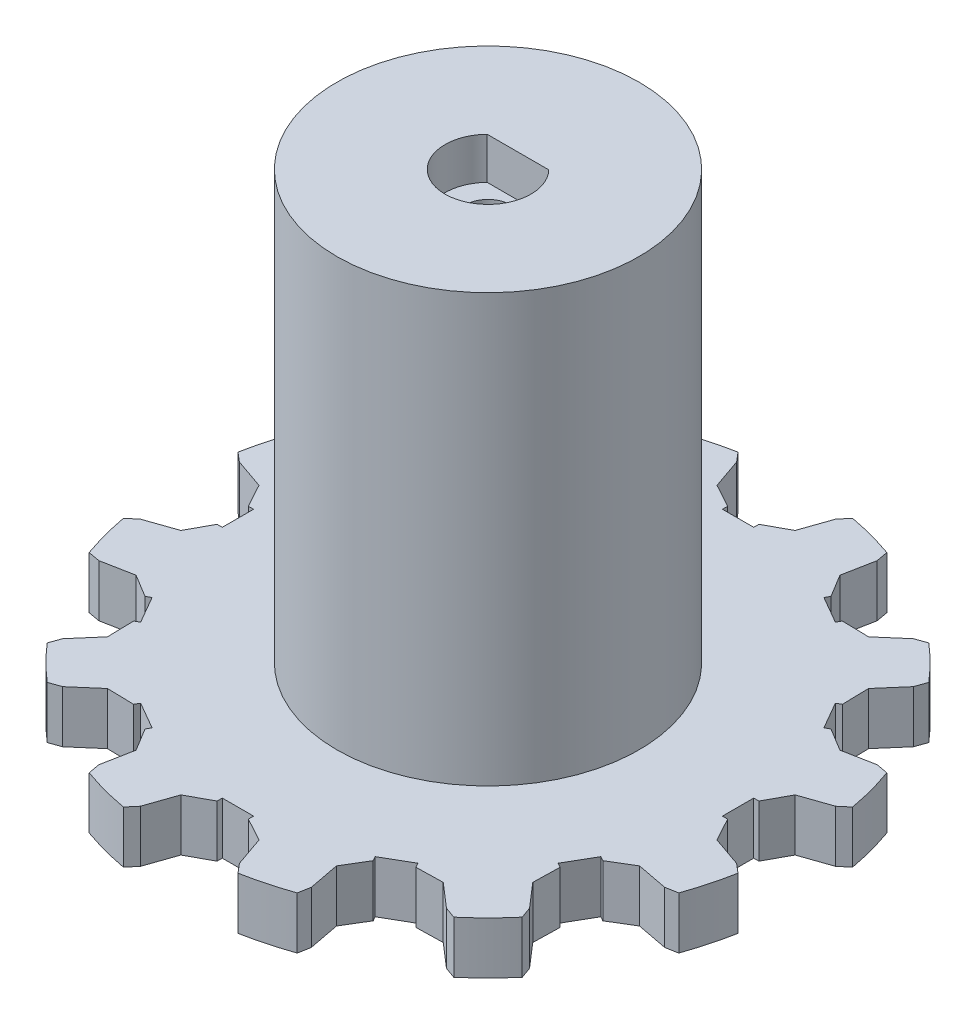
SolidWorks part; units mm, degrees
ref_plane "Front Plane" through (0, 0, 0) normal (0, 0, 1) x (1, 0, 0)
ref_plane "Top Plane" through (0, 0, 0) normal (0, 1, 0) x (1, 0, 0)
ref_plane "Right Plane" through (0, 0, 0) normal (1, 0, 0) x (0, 0, -1)
sketch "Sketch1" plane through (0, 0, 0) normal (0, 1, 0) x (1, 0, 0)
  line L0 (0, -1000) -> (0, 49000) construction
  line L1 (-3.75, 25.7281) -> (-4.75, 28.6083)
  line L2 (3.75, 25.7281) -> (4.75, 28.6083)
  line L3 (-3.75, 25.7281) -> (-1.5, 24.4948)
  line L4 (1.5, 24) -> (-1.5, 24)
  line L8 (-1.5, 24) -> (-1.5, 24.4948)
  line L9 (1.5, 24) -> (1.5, 24.4948)
  line L10 (3.75, 25.7281) -> (1.5, 24.4948)
  line L11 (4.75, 28.6083) -> (5.5, 29.4915)
  line L12 (-4.75, 28.6083) -> (-5.5, 29.4915)
  line L13 (18.4178, 22.4006) -> (19.5089, 22.7904)
  line L14 (16.1117, 20.4062) -> (18.4178, 22.4006)
  line L15 (16.1117, 20.4062) -> (13.5464, 20.4631)
  line L16 (13.299, 20.0346) -> (13.5464, 20.4631)
  line L17 (13.299, 20.0346) -> (10.701, 21.5346)
  line L18 (10.701, 21.5346) -> (10.9484, 21.9631)
  line L19 (9.6165, 24.1562) -> (10.9484, 21.9631)
  line L20 (9.6165, 24.1562) -> (10.1906, 27.1506)
  line L21 (10.1906, 27.1506) -> (9.9826, 28.2904)
  line L22 (27.1506, 10.1906) -> (28.2904, 9.9826)
  line L23 (24.1562, 9.6165) -> (27.1506, 10.1906)
  line L24 (24.1562, 9.6165) -> (21.9631, 10.9484)
  line L25 (21.5346, 10.701) -> (21.9631, 10.9484)
  line L26 (21.5346, 10.701) -> (20.0346, 13.299)
  line L27 (20.0346, 13.299) -> (20.4631, 13.5464)
  line L28 (20.4062, 16.1117) -> (20.4631, 13.5464)
  line L29 (20.4062, 16.1117) -> (22.4006, 18.4178)
  line L30 (22.4006, 18.4178) -> (22.7904, 19.5089)
  line L31 (28.6083, -4.75) -> (29.4915, -5.5)
  line L32 (25.7281, -3.75) -> (28.6083, -4.75)
  line L33 (25.7281, -3.75) -> (24.4948, -1.5)
  line L34 (24, -1.5) -> (24.4948, -1.5)
  line L35 (24, -1.5) -> (24, 1.5)
  line L36 (24, 1.5) -> (24.4948, 1.5)
  line L37 (25.7281, 3.75) -> (24.4948, 1.5)
  line L38 (25.7281, 3.75) -> (28.6083, 4.75)
  line L39 (28.6083, 4.75) -> (29.4915, 5.5)
  line L40 (22.4006, -18.4178) -> (22.7904, -19.5089)
  line L41 (20.4062, -16.1117) -> (22.4006, -18.4178)
  line L42 (20.4062, -16.1117) -> (20.4631, -13.5464)
  line L43 (20.0346, -13.299) -> (20.4631, -13.5464)
  line L44 (20.0346, -13.299) -> (21.5346, -10.701)
  line L45 (21.5346, -10.701) -> (21.9631, -10.9484)
  line L46 (24.1562, -9.6165) -> (21.9631, -10.9484)
  line L47 (24.1562, -9.6165) -> (27.1506, -10.1906)
  line L48 (27.1506, -10.1906) -> (28.2904, -9.9826)
  line L49 (10.1906, -27.1506) -> (9.9826, -28.2904)
  line L50 (9.6165, -24.1562) -> (10.1906, -27.1506)
  line L51 (9.6165, -24.1562) -> (10.9484, -21.9631)
  line L52 (10.701, -21.5346) -> (10.9484, -21.9631)
  line L53 (10.701, -21.5346) -> (13.299, -20.0346)
  line L54 (13.299, -20.0346) -> (13.5464, -20.4631)
  line L55 (16.1117, -20.4062) -> (13.5464, -20.4631)
  line L56 (16.1117, -20.4062) -> (18.4178, -22.4006)
  line L57 (18.4178, -22.4006) -> (19.5089, -22.7904)
  line L58 (-4.75, -28.6083) -> (-5.5, -29.4915)
  line L59 (-3.75, -25.7281) -> (-4.75, -28.6083)
  line L60 (-3.75, -25.7281) -> (-1.5, -24.4948)
  line L61 (-1.5, -24) -> (-1.5, -24.4948)
  line L62 (-1.5, -24) -> (1.5, -24)
  line L63 (1.5, -24) -> (1.5, -24.4948)
  line L64 (3.75, -25.7281) -> (1.5, -24.4948)
  line L65 (3.75, -25.7281) -> (4.75, -28.6083)
  line L66 (4.75, -28.6083) -> (5.5, -29.4915)
  line L67 (-18.4178, -22.4006) -> (-19.5089, -22.7904)
  line L68 (-16.1117, -20.4062) -> (-18.4178, -22.4006)
  line L69 (-16.1117, -20.4062) -> (-13.5464, -20.4631)
  line L70 (-13.299, -20.0346) -> (-13.5464, -20.4631)
  line L71 (-13.299, -20.0346) -> (-10.701, -21.5346)
  line L72 (-10.701, -21.5346) -> (-10.9484, -21.9631)
  line L73 (-9.6165, -24.1562) -> (-10.9484, -21.9631)
  line L74 (-9.6165, -24.1562) -> (-10.1906, -27.1506)
  line L75 (-10.1906, -27.1506) -> (-9.9826, -28.2904)
  line L76 (-27.1506, -10.1906) -> (-28.2904, -9.9826)
  line L77 (-24.1562, -9.6165) -> (-27.1506, -10.1906)
  line L78 (-24.1562, -9.6165) -> (-21.9631, -10.9484)
  line L79 (-21.5346, -10.701) -> (-21.9631, -10.9484)
  line L80 (-21.5346, -10.701) -> (-20.0346, -13.299)
  line L81 (-20.0346, -13.299) -> (-20.4631, -13.5464)
  line L82 (-20.4062, -16.1117) -> (-20.4631, -13.5464)
  line L83 (-20.4062, -16.1117) -> (-22.4006, -18.4178)
  line L84 (-22.4006, -18.4178) -> (-22.7904, -19.5089)
  line L85 (-28.6083, 4.75) -> (-29.4915, 5.5)
  line L86 (-25.7281, 3.75) -> (-28.6083, 4.75)
  line L87 (-25.7281, 3.75) -> (-24.4948, 1.5)
  line L88 (-24, 1.5) -> (-24.4948, 1.5)
  line L89 (-24, 1.5) -> (-24, -1.5)
  line L90 (-24, -1.5) -> (-24.4948, -1.5)
  line L91 (-25.7281, -3.75) -> (-24.4948, -1.5)
  line L92 (-25.7281, -3.75) -> (-28.6083, -4.75)
  line L93 (-28.6083, -4.75) -> (-29.4915, -5.5)
  line L94 (-22.4006, 18.4178) -> (-22.7904, 19.5089)
  line L95 (-20.4062, 16.1117) -> (-22.4006, 18.4178)
  line L96 (-20.4062, 16.1117) -> (-20.4631, 13.5464)
  line L97 (-20.0346, 13.299) -> (-20.4631, 13.5464)
  line L98 (-20.0346, 13.299) -> (-21.5346, 10.701)
  line L99 (-21.5346, 10.701) -> (-21.9631, 10.9484)
  line L100 (-24.1562, 9.6165) -> (-21.9631, 10.9484)
  line L101 (-24.1562, 9.6165) -> (-27.1506, 10.1906)
  line L102 (-27.1506, 10.1906) -> (-28.2904, 9.9826)
  line L103 (-10.1906, 27.1506) -> (-9.9826, 28.2904)
  line L104 (-9.6165, 24.1562) -> (-10.1906, 27.1506)
  line L105 (-9.6165, 24.1562) -> (-10.9484, 21.9631)
  line L106 (-10.701, 21.5346) -> (-10.9484, 21.9631)
  line L107 (-10.701, 21.5346) -> (-13.299, 20.0346)
  line L108 (-13.299, 20.0346) -> (-13.5464, 20.4631)
  line L109 (-16.1117, 20.4062) -> (-13.5464, 20.4631)
  line L110 (-16.1117, 20.4062) -> (-18.4178, 22.4006)
  line L111 (-18.4178, 22.4006) -> (-19.5089, 22.7904)
  circle A0 centre (0, 0) radius 25 construction
  circle A1 centre (0, 0) radius 26 construction
  circle A2 centre (0, 0) radius 30 construction
  circle A3 centre (0, 0) radius 29 construction
  arc A4 (5.5, 29.4915) -> (8, 28.9137) centre (0, 0) cw
  arc A5 (-5.5, 29.4915) -> (-8, 28.9137) centre (0, 0) ccw
  arc A6 (19.5089, 22.7904) -> (21.385, 21.04) centre (0, 0) cw
  arc A7 (9.9826, 28.2904) -> (7.5286, 29.04) centre (0, 0) ccw
  arc A8 (28.2904, 9.9826) -> (29.04, 7.5286) centre (0, 0) cw
  arc A9 (22.7904, 19.5089) -> (21.04, 21.385) centre (0, 0) ccw
  arc A10 (29.4915, -5.5) -> (28.9137, -8) centre (0, 0) cw
  arc A11 (29.4915, 5.5) -> (28.9137, 8) centre (0, 0) ccw
  arc A12 (22.7904, -19.5089) -> (21.04, -21.385) centre (0, 0) cw
  arc A13 (28.2904, -9.9826) -> (29.04, -7.5286) centre (0, 0) ccw
  arc A14 (9.9826, -28.2904) -> (7.5286, -29.04) centre (0, 0) cw
  arc A15 (19.5089, -22.7904) -> (21.385, -21.04) centre (0, 0) ccw
  arc A16 (-5.5, -29.4915) -> (-8, -28.9137) centre (0, 0) cw
  arc A17 (5.5, -29.4915) -> (8, -28.9137) centre (0, 0) ccw
  arc A18 (-19.5089, -22.7904) -> (-21.385, -21.04) centre (0, 0) cw
  arc A19 (-9.9826, -28.2904) -> (-7.5286, -29.04) centre (0, 0) ccw
  arc A20 (-28.2904, -9.9826) -> (-29.04, -7.5286) centre (0, 0) cw
  arc A21 (-22.7904, -19.5089) -> (-21.04, -21.385) centre (0, 0) ccw
  arc A22 (-29.4915, 5.5) -> (-28.9137, 8) centre (0, 0) cw
  arc A23 (-29.4915, -5.5) -> (-28.9137, -8) centre (0, 0) ccw
  arc A24 (-22.7904, 19.5089) -> (-21.04, 21.385) centre (0, 0) cw
  arc A25 (-28.2904, 9.9826) -> (-29.04, 7.5286) centre (0, 0) ccw
  arc A26 (-9.9826, 28.2904) -> (-7.5286, 29.04) centre (0, 0) cw
  arc A27 (-19.5089, 22.7904) -> (-21.385, 21.04) centre (0, 0) ccw
  point P12 (0, 25)
  point P156 (0, 0)
  dimension "D1" = 50
  dimension "D2" = 52
  dimension "D3" = 60
  dimension "D4" = 58
  dimension "D5" = 3.75
  dimension "D6" = 4.75
  dimension "D8" = 4.75
  dimension "D10" = 3
  dimension "D7" = 3.75
  dimension "D9" = 25
  dimension "D11" = 1.5
  dimension "D12" = 24
  dimension "D13" = 118.729
  dimension "D14" = 118.729
  dimension "D15" = 5.5
  dimension "D16" = 5.5
  dimension "D17" = 8
  dimension "D18" = 8
  dimension "D19" = 12
extrude "Boss-Extrude1" add sketch "Sketch1" along normal blind 5 contours L111 A27 A24 L94 L95 L96 L97 L98 L99 L100 L101 L102 A25 A22 L85 L86 L87 L88 L89 L90 L91 L92 L93 A23 A20 L76 L77 L78 L79 L80 L81 L82 L83 L84 A21 A18 L67 L68 L69 L70 L71 L72 L73 L74 L75 A19 A16
sketch "Sketch2" plane through (0, 5, 0) normal (0, 1, 0) x (1, 0, 0)
  circle A0 centre (0, 0) radius 14.5
  dimension "D1" = 29
extrude "Boss-Extrude3" add sketch "Sketch2" along normal blind 41
sketch "Sketch4" plane through (0, 46, 0) normal (0, 1, 0) x (1, 0, 0)
  line L1 (2.958, 5.375) -> (-2.958, 5.375)
  line L2 (2.958, 5.375) -> (2.958, 2.875)
  line L3 (2.958, 2.875) -> (-2.958, 2.875)
  line L4 (-2.958, 5.375) -> (-2.958, 2.875)
  line L5 (2.958, 5.375) -> (-2.958, 2.875) construction
  line L6 (2.958, 2.875) -> (-2.958, 5.375) construction
  circle A0 centre (0, 0) radius 4.125
  point P3 (0, 4.125)
  dimension "D1" = 8.25
  dimension "D2" = 2.5
extrude "Cut-Extrude2" cut sketch "Sketch4" against normal blind 4 contours L3 A0
sketch "Sketch10" plane through (0, 0, 0) normal (0, -1, 0) x (1, 0, 0)
  circle A0 centre (0, 0) radius 2.125
  dimension "D1" = 4.25
extrude "Cut-Extrude4" cut sketch "Sketch10" against normal through all both and the other way through all
sketch "Sketch11" plane through (0, 0, 0) normal (0, -1, 0) x (-1, 0, 0)
  circle A0 centre (0, 0) radius 3.625
  dimension "D1" = 7.25
extrude "Cut-Extrude5" cut sketch "Sketch11" against normal blind 10
